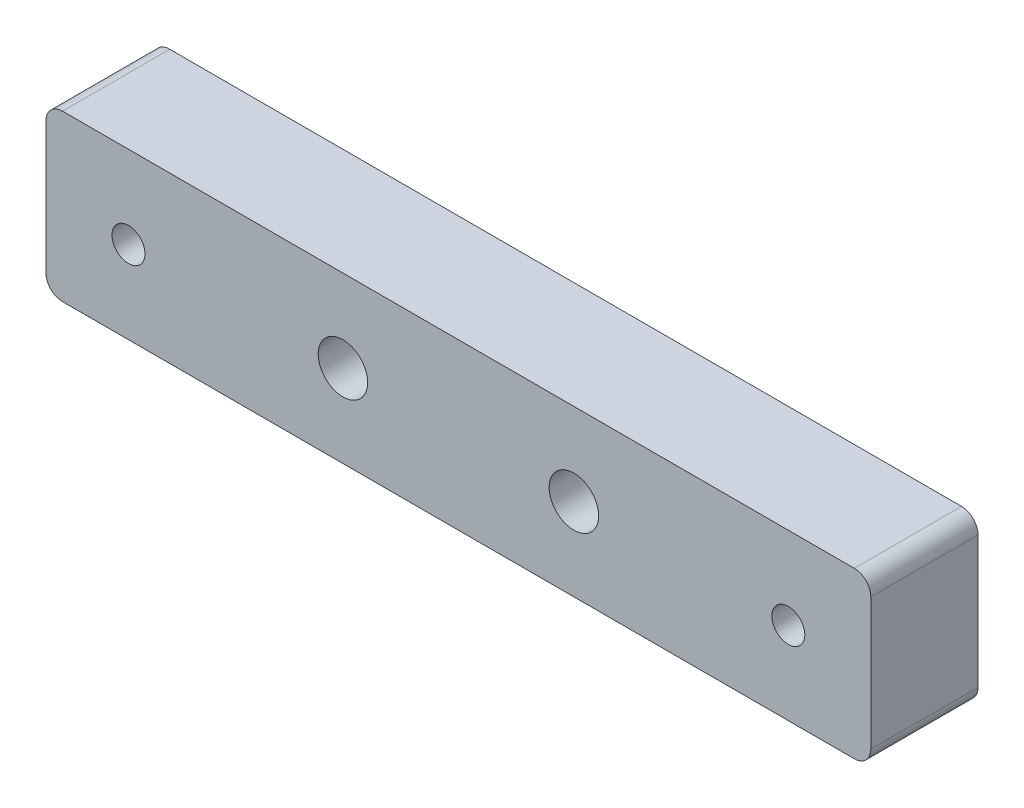
SolidWorks part; units mm, degrees
ref_plane "Front Plane" through (0, 0, 0) normal (0, 0, 1) x (1, 0, 0)
ref_plane "Top Plane" through (0, 0, 0) normal (0, 1, 0) x (1, 0, 0)
ref_plane "Right Plane" through (0, 0, 0) normal (1, 0, 0) x (0, 0, -1)
sketch "Sketch1" plane through (0, 0, 0) normal (0, 0, 1) x (1, 0, 0)
  line L1 (0, 0) -> (100, 0)
  line L2 (0, 0) -> (0, 20)
  line L3 (0, 20) -> (100, 20)
  line L4 (100, 0) -> (100, 20)
  dimension "D1" = 100
  dimension "D2" = 20
extrude "Boss-Extrude1" add sketch "Sketch1" along normal blind 13
sketch "Sketch2" plane through (0, 0, 13) normal (0, 0, 1) x (1, 0, 0)
  line L0 (0, 10) -> (100, 10) construction
  line L1 (0, 20) -> (0, 0) construction
  line L2 (100, 0) -> (100, 20) construction
  line L3 (50, 20) -> (50, 0) construction
  line L4 (100, 20) -> (0, 20) construction
  line L5 (0, 0) -> (100, 0) construction
  circle A0 centre (64, 10) radius 3
  circle A1 centre (36, 10) radius 3
  circle A2 centre (10, 10) radius 2
  circle A3 centre (90, 10) radius 2
  dimension "D1" = 6
  dimension "D3" = 4
  dimension "D2" = 28
  dimension "D4" = 80
extrude "Cut-Extrude1" cut sketch "Sketch2" against normal blind 13
sketch "Sketch3" plane through (0, 0, 13) normal (0, 0, 1) x (1, 0, 0)
  line L1 (2, 0) -> (98, 0)
  line L2 (0, 2) -> (0, 18)
  line L3 (2, 20) -> (98, 20)
  line L4 (100, 2) -> (100, 18)
  line L5 (0, 20) -> (100, 20)
  line L6 (0, 20) -> (0, 0)
  line L7 (0, 0) -> (100, 0)
  line L8 (100, 20) -> (100, 0)
  arc A0 (100, 18) -> (98, 20) centre (98, 18) ccw
  arc A1 (98, 0) -> (100, 2) centre (98, 2) ccw
  arc A2 (0, 2) -> (2, 0) centre (2, 2) ccw
  arc A3 (0, 18) -> (2, 20) centre (2, 18) cw
  point P8 (100, 20)
  point P13 (0, 0)
  line M13 (0, 20) -> (0, 0)
  line M14 (0, 0) -> (100, 0)
  line M15 (100, 0) -> (100, 20)
  line M16 (100, 20) -> (0, 20)
  dimension "D1" = 2
extrude "Cut-Extrude2" cut sketch "Sketch3" against normal blind 13 contours A0 M15 M16 | A1 M14 M15 | A2 M13 M14 | A3 M13 M16
